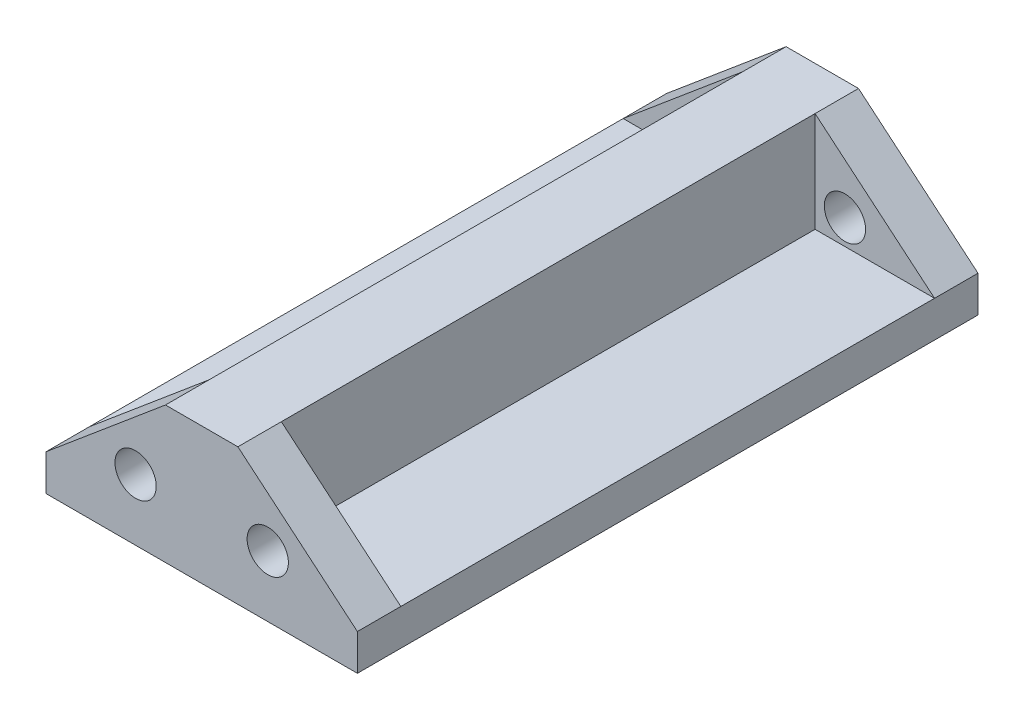
SolidWorks part; units mm, degrees
material "ABS"
ref_plane "Front Plane" through (0, 0, 0) normal (0, 0, 1) x (1, 0, 0)
ref_plane "Top Plane" through (0, 0, 0) normal (0, 1, 0) x (1, 0, 0)
ref_plane "Right Plane" through (0, 0, 0) normal (1, 0, 0) x (0, 0, -1)
sketch "Sketch1" plane through (0, 0, 0) normal (0, 0, 1) x (1, 0, 0)
  line L0 (21.5, -4.4226) -> (5, 9.4226)
  line L1 (5, 9.4226) -> (-5, 9.4226)
  line L2 (-5, 9.4226) -> (-21.5, -4.4226)
  line L3 (-21.5, -4.4226) -> (-21.5, -9.4226)
  line L4 (-21.5, -9.4226) -> (21.5, -9.4226)
  line L5 (21.5, -9.4226) -> (21.5, -4.4226)
  line L6 (0, 13.92) -> (0, -13.0366) construction
  line L7 (-22.2232, 0) -> (22.9412, 0) construction
  circle A0 centre (9.125, -0.9613) radius 2.85
  circle A1 centre (-9.125, -0.9613) radius 2.85
  point P13 (0, 9.4226)
  dimension "D15" = 5.7
  dimension "D1" = 5
  dimension "D2" = 12.375
  dimension "D3" = 3.4613
  dimension "D4" = 18.25
  dimension "D5" = 43
  dimension "D6" = 10
  dimension "D7" = 9.4226
  dimension "D8" = 21.5392
  dimension "D9" = 18.8451
  dimension "D10" = 40
  dimension "D11" = 40
  dimension "D12" = 21.5
  dimension "D13" = 9.125
  dimension "D14" = 0.9613
extrude "Boss-Extrude1" add sketch "Sketch1" along normal blind 85.7063 contours L4 L5 L0 L1 L2 L3 A1 A0 | A1 | A0
sketch "Sketch2" plane through (0, 0, 0) normal (0, 0, -1) x (-1, 0, 0)
  line L0 (5, 9.4226) -> (21.5, -4.4226) construction
  line L1 (-21.5, -4.4226) -> (-5, 9.4226) construction
  line L2 (5, 9.4226) -> (21.5, -4.4226)
  line L3 (-21.5, -4.4226) -> (-5, 9.4226)
  line L4 (-21.5, -4.4226) -> (-5, -4.4226)
  line L5 (-5, -4.4226) -> (-5, 9.4226)
  line L6 (5, 9.4226) -> (5, -4.4226)
  line L7 (5, -4.4226) -> (21.5, -4.4226)
extrude "Cut-Extrude1" cut sketch "Sketch2" against normal offset from surface (73.7063 mm away) 6 from offset 6 up to face at (0, -1.4742, 85.7063) offset against normal yes
sketch "Sketch3" plane through (0, 0, 0) normal (0, 0, -1) x (-1, 0, 0)
  circle A0 centre (9.125, -0.9613) radius 2.85 construction
  circle A1 centre (-9.125, -0.9613) radius 2.85 construction
  circle A2 centre (9.125, -0.9613) radius 2.85
  circle A3 centre (-9.125, -0.9613) radius 2.85
extrude "Cut-Extrude2" cut sketch "Sketch3" against normal through all
sketch "Sketch4" plane through (0, 9.4226, 0) normal (0, 1, 0) x (1, 0, 0)
  line L0 (21.5, -79.7063) -> (21.5, -6) construction
  line L1 (-21.5, -79.7063) -> (-21.5, -6) construction
  line L2 (21.5, -79.7063) -> (21.5, -6)
  line L3 (-21.5, -79.7063) -> (-21.5, -6)
  line L4 (-21.5, -42.8532) -> (21.5, -42.8532) construction
  point P6 (0, -42.8532)
